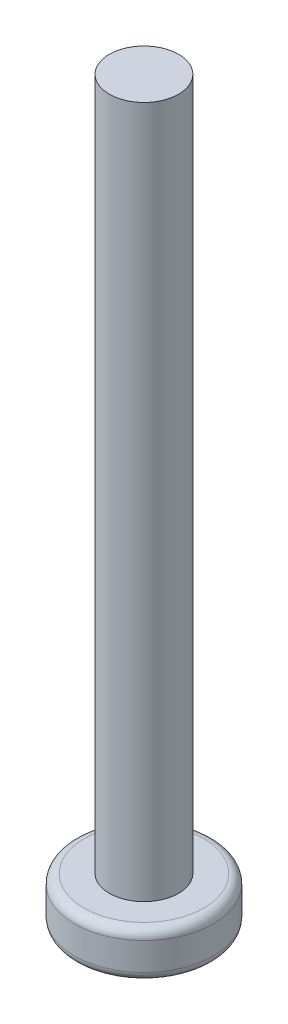
SolidWorks part; units mm, degrees
ref_plane "Front Plane" through (0, 0, 0) normal (0, 0, 1) x (1, 0, 0)
ref_plane "Top Plane" through (0, 0, 0) normal (0, 1, 0) x (1, 0, 0)
ref_plane "Right Plane" through (0, 0, 0) normal (1, 0, 0) x (0, 0, -1)
sketch "Sketch1" plane through (0, 0, 0) normal (0, 1, 0) x (1, 0, 0)
  circle A0 centre (0, 0) radius 3
  dimension "D1" = 6
extrude "Boss-Extrude1" add sketch "Sketch1" along normal blind 2
sketch "Sketch2" plane through (0, 2, 0) normal (0, 1, 0) x (1, 0, 0)
  circle A0 centre (0, 0) radius 1.5
  dimension "D1" = 3
extrude "Boss-Extrude2" add sketch "Sketch2" along normal blind 30
sketch "Sketch3" plane through (0, 0, 0) normal (0, -1, 0) x (-1, 0, 0)
  line L1 (0.45, -1.5) -> (-0.45, -1.5)
  line L2 (0.45, -1.5) -> (0.45, 1.5)
  line L3 (0.45, 1.5) -> (-0.45, 1.5)
  line L4 (-0.45, -1.5) -> (-0.45, 1.5)
  line L5 (1.5, -0.45) -> (-1.5, -0.45)
  line L6 (1.5, -0.45) -> (1.5, 0.45)
  line L7 (1.5, 0.45) -> (-1.5, 0.45)
  line L8 (-1.5, -0.45) -> (-1.5, 0.45)
  point P4 (0, -1.5)
  point P5 (0, 1.5)
  point P14 (1.5, 0)
  point P15 (-1.5, 0)
  dimension "D1" = 1.5
  dimension "D2" = 1.5
  dimension "D3" = 0.9
  dimension "D4" = 0.9
  dimension "D5" = 1.5
  dimension "D6" = 1.5
extrude "Cut-Extrude1" cut sketch "Sketch3" against normal blind 1.9 contours L2 L7 L4 L5 | L6 L7 L2 L5 | L2 L5 L4 L1 | L8 L5 L4 L7 | L7 L2 L3 L4
fillet "Fillet1" radius 0.4 2 edges at (0, 2, 3) (0, 0, 3)
